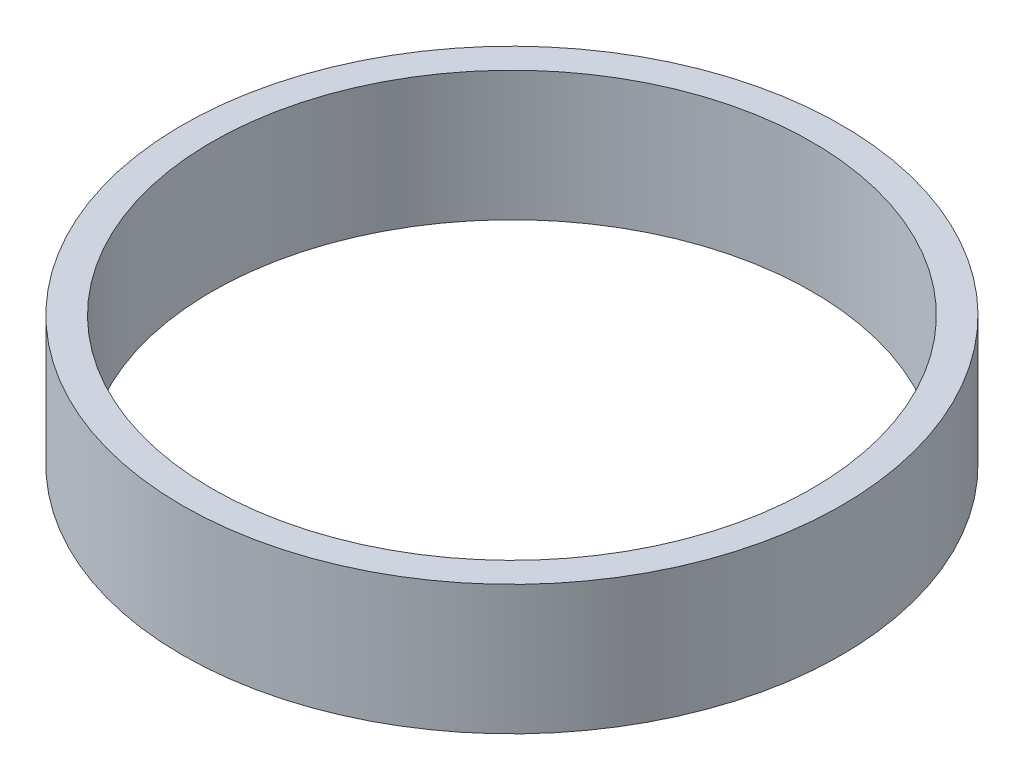
SolidWorks part; units mm, degrees
ref_plane "前视基准面" through (0, 0, 0) normal (0, 0, 1) x (1, 0, 0)
ref_plane "上视基准面" through (0, 0, 0) normal (0, 1, 0) x (1, 0, 0)
ref_plane "右视基准面" through (0, 0, 0) normal (1, 0, 0) x (0, 0, -1)
sketch "草图1" plane through (0, 0, 0) normal (0, 1, 0) x (1, 0, 0)
  circle A0 centre (0, 0) radius 25.5
  circle A1 centre (0, 0) radius 28
  dimension "D1" = 56
  dimension "D2" = 51
extrude "凸台-拉伸1" add sketch "草图1" along normal blind 11
cosmetic thread "装饰螺纹线1" parameters "D1"=5, "D2"=52
